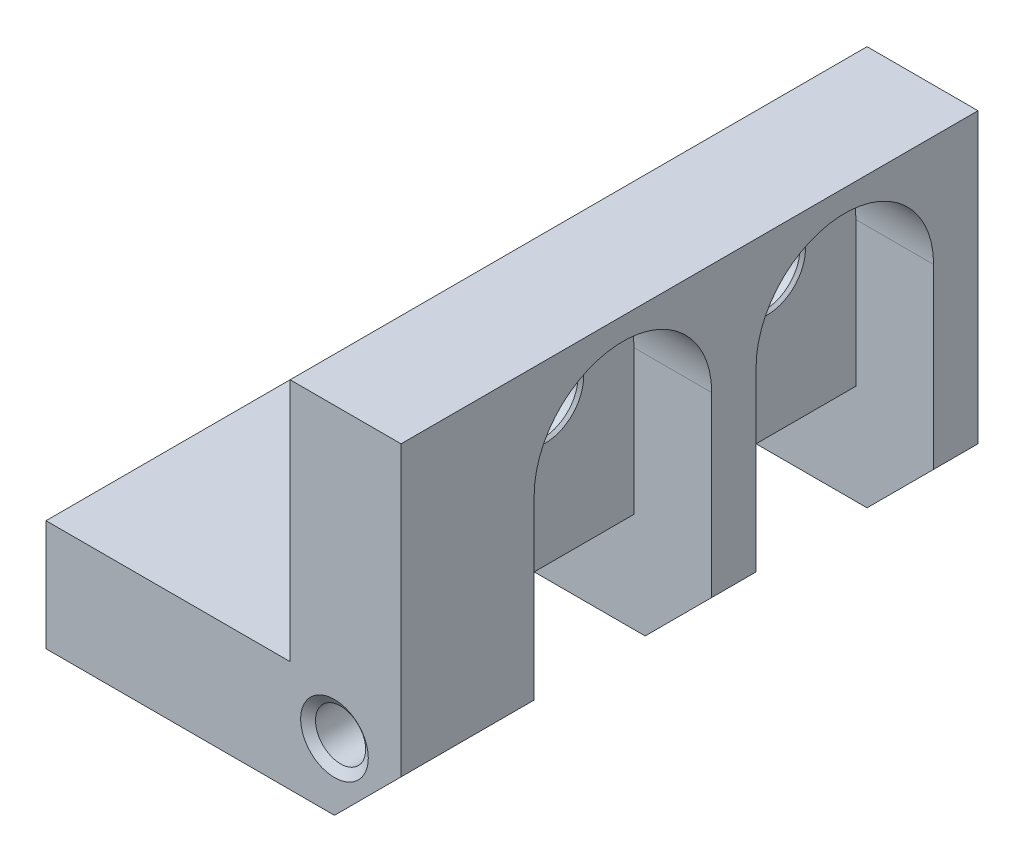
SolidWorks part; units mm, degrees
material "6063-T1"
ref_plane "Спереди" through (0, 0, 0) normal (0, 0, 1) x (1, 0, 0)
ref_plane "Сверху" through (0, 0, 0) normal (0, 1, 0) x (1, 0, 0)
ref_plane "Справа" through (0, 0, 0) normal (1, 0, 0) x (0, 0, -1)
sketch "Эскиз1" plane through (0, 0, 0) normal (0, 0, 1) x (1, 0, 0)
  line L1 (-8, -8) -> (8, -8)
  line L2 (-8, -8) -> (-8, 8)
  line L3 (-8, 8) -> (8, 8)
  line L4 (8, -8) -> (8, 8)
  line L5 (-8, -8) -> (8, 8) construction
  line L6 (-8, 8) -> (8, -8) construction
  point P0 (0, 0)
  dimension "D2" = 16
extrude "Вытянуть1" add sketch "Эскиз1" along normal blind 26
sketch "Эскиз2" plane through (0, 0, 0) normal (0, 0, -1) x (-1, 0, 0)
  line L0 (-3, 8) -> (-3, -3)
  line L1 (-3, -3) -> (8, -3)
  line L3 (8, 8) -> (8, -8) construction
  line L4 (-8, 8) -> (8, 8) construction
  line L5 (-8, -8) -> (-8, 8) construction
  line L6 (8, -8) -> (-8, -8) construction
  dimension "D1" = 5
  dimension "D2" = 5
extrude "Вырез-Вытянуть1" cut sketch "Эскиз2" against normal through all
sketch "Эскиз9" plane through (8, 0, 0) normal (1, 0, 0) x (0, 0, -1)
  line L0 (-20, -8) -> (-20, 3)
  line L1 (-26, -8) -> (0, -8) construction
  line L2 (-12, -8) -> (-12, 3)
  line L3 (-10, -8) -> (-10, 3)
  line L4 (-2, -8) -> (-2, 3)
  line L5 (-26, -8) -> (-26, 8) construction
  line L6 (-26, -3) -> (0, -3) construction
  arc A0 (-10, 3) -> (-2, 3) centre (-6, 3) cw
  arc A1 (-12, 3) -> (-20, 3) centre (-16, 3) ccw
  line M4 (-26, -8) -> (0, -8)
  dimension "D1" = 6
  dimension "D2" = 4
  dimension "D3" = 10
  dimension "D4" = 10
extrude "Вырез-Вытянуть2" cut sketch "Эскиз9" against normal offset from surface (3.5 mm away) 1.5 contours L2 A1 L0 M4 | A0 L3 L4 M4 up to face at (3, 2.5, 13)
sketch "Эскиз10" plane through (0, -8, 0) normal (0, -1, 0) x (1, 0, 0)
  line L0 (4.5, 20) -> (-3, 20)
  line L1 (4.5, 12) -> (-3, 12)
  line L2 (4.5, 10) -> (-3, 10)
  line L3 (4.5, 2) -> (-3, 2)
  line L5 (3, 26) -> (3, 0) construction
  arc A0 (-3, 20) -> (-3, 12) centre (-3, 16) ccw
  arc A1 (-3, 10) -> (-3, 2) centre (-3, 6) ccw
  line M4 (4.5, 12) -> (4.5, 20)
  line M12 (4.5, 2) -> (4.5, 10)
  dimension "D1" = 6
extrude "Вырез-Вытянуть3" cut sketch "Эскиз10" against normal offset from surface (3.5 mm away) 1.5 contours L0 A0 L1 M4 | L2 A1 L3 M12 up to face at (-2.5, -3, 13)
chamfer "Фаска1" distance 1 angle 45 2 edges at (4.5, -4.5, 6) (4.5, -4.5, 16)
hole_wizard "Отверстие обработанное метчиком #4-401" positions "Эскиз8" profile "Эскиз7" tap size "#4-40" standard "Ansi (в дюймах)"
sketch "Эскиз8" plane through (-3.0544, -0.9842, 26) normal (0, 0, -1) x (-1, 0, 0)
  line L0 (-6.0544, 8.9842) -> (-6.0544, -2.0158) construction
  line L1 (-6.0544, -2.0158) -> (4.9456, -2.0158) construction
  point P0 (-8.0544, -4.0158)
  dimension "D1" = 2
  dimension "D2" = 2
sketch "Эскиз7" plane through (5, -5, 26) normal (1, 0, 0) x (0, -1, 0)
  line L0 (0, 0) -> (0, 6)
  line L1 (0, 6) -> (1.1303, 6)
  line L2 (1.1303, 6) -> (1.1303, 0.2757)
  line L3 (1.1303, 0.2757) -> (1.524, 0)
  line L5 (1.524, 0) -> (0, 0)
  line L6 (-1.1303, 0.2757) -> (-1.524, 0) construction
  line L11 (0, -6.35) -> (0, 107.95) construction
  dimension "Диаметр проходного сверла" = 2.2606
  dimension "Глубина проходного сверла" = 6
  dimension "Диаметр передней зенковки" = 3.048
  dimension "Угол передней зенковки" = 110
cosmetic thread "Отверстие резьбы1" parameters "D2"=2.8448
hole_wizard "Отверстие с зазором M31" positions "Трехмерный эскиз1" profile "Эскиз11" hole size "M3" standard "Ansi (метрические)" end condition up to next
sketch3d "Трехмерный эскиз1"
  line L0 (-3, -4.5, 6) -> (-3, -8, 6) construction
  arc A0 (4.5, 3, 20) -> (4.5, 3, 12) centre (4.5, 3, 16) ccw construction
  arc A1 (4.5, 3, 2) -> (4.5, 3, 10) centre (4.5, 3, 6) ccw construction
  arc A2 (-3, -4.5, 12) -> (-3, -4.5, 20) centre (-3, -4.5, 16) ccw construction
  arc A3 (-3, -4.5, 2) -> (-3, -4.5, 10) centre (-3, -4.5, 6) ccw construction
  point P0 (-3, -4.5, 16)
  point P2 (-3, -4.5, 6)
  point P6 (4.5, 3, 6)
  point P8 (4.5, 3, 16)
  point P14 (0.5, 3, 16)
  point P18 (8.5, 3, 6)
  point P22 (-3, -0.5, 16)
  point P26 (-3, -0.5, 6)
sketch "Эскиз11" plane through (-3, -4.5, 16) normal (1, 0, 0) x (0, 0, -1)
  line L0 (0, 0) -> (0, 1.5)
  line L1 (0, 1.5) -> (1.725, 1.5)
  line L2 (1.6, 1.375) -> (1.6, 0.125)
  line L3 (1.6, 0.125) -> (1.725, 0)
  line L5 (1.725, 0) -> (0, 0)
  line L6 (-1.6, 0.125) -> (-1.725, 0) construction
  line L7 (1.725, 1.5) -> (1.6, 1.375)
  line L8 (-1.725, 1.5) -> (-1.6, 1.375) construction
  line L11 (0, -6.35) -> (0, 107.95) construction
  dimension "Диаметр сквозного отверстия" = 3.2
  dimension "Глубина сквозного отверстия" = 1.5
  dimension "Диаметр передней зенковки" = 3.45
  dimension "Угол передней зенковки" = 90
  dimension "Диаметр задней зенковки" = 3.45
  dimension "Угол задней зенковки" = 90
chamfer "Фаска3" distance 3 angle 45 3 edges at (8, -8, 1) (8, -8, 11) (8, -8, 23)
